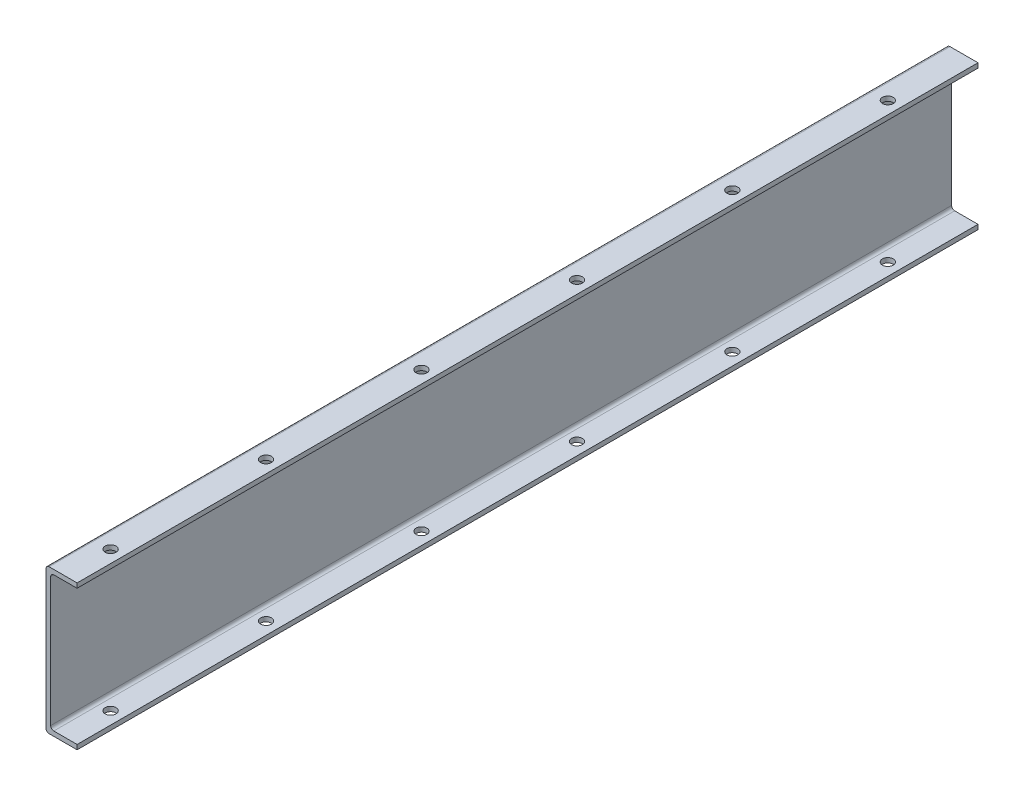
SolidWorks part; units mm, degrees
material "6061-T6 (SS)"
ref_plane "Front Plane" through (0, 0, 0) normal (0, 0, 1) x (1, 0, 0)
ref_plane "Top Plane" through (0, 0, 0) normal (0, 1, 0) x (1, 0, 0)
ref_plane "Right Plane" through (0, 0, 0) normal (1, 0, 0) x (0, 0, -1)
sketch "Sketch1" plane through (0, 0, 0) normal (0, 0, 1) x (1, 0, 0)
  line L1 (-0.75, 21.75) -> (0.75, 21.75)
  line L2 (-0.75, 21.75) -> (-0.75, -21.75)
  line L3 (-0.75, -21.75) -> (0.75, -21.75)
  line L4 (0.75, 21.75) -> (0.75, -21.75)
  line L5 (-0.75, 21.75) -> (9.25, 21.75)
  line L6 (-0.75, 21.75) -> (-0.75, 23.25)
  line L7 (-0.75, 23.25) -> (9.25, 23.25)
  line L8 (9.25, 21.75) -> (9.25, 23.25)
  line L9 (-0.75, -21.75) -> (9.25, -21.75)
  line L10 (-0.75, -21.75) -> (-0.75, -23.25)
  line L11 (-0.75, -23.25) -> (9.25, -23.25)
  line L12 (9.25, -21.75) -> (9.25, -23.25)
  dimension "D1" = 43.5
  dimension "D2" = 1.5
  dimension "D3" = 0.75
  dimension "D4" = 21.75
  dimension "D5" = 1.5
  dimension "D6" = 10
  dimension "D7" = 1.5
  dimension "D8" = 10
extrude "Boss-Extrude1" add sketch "Sketch1" along normal blind 289.77 contours L4 L1 L2 L3 | L5 L8 L7 L6 L1 | L12 L9 L3 L10 L11
fillet "Fillet1" radius 1 4 edges at (0.75, -21.75, 144.885) (0.75, 21.75, 144.885) (-0.75, 23.25, 144.885) (-0.75, -23.25, 144.885)
sketch "Sketch3" plane through (0, -23.25, 0) normal (0, -1, 0) x (-1, 0, 0)
  line L0 (-5.25, 0) -> (-5.25, -289.77) construction
  line L1 (-0.25, 0) -> (-9.25, 0) construction
  line L2 (-0.25, -289.77) -> (-9.25, -289.77) construction
  line L4 (-0.25, -289.77) -> (-0.25, 0) construction
  circle A0 centre (-5.25, -25) radius 1.75
  circle A1 centre (-5.25, -75) radius 1.75
  circle A2 centre (-5.25, -125) radius 1.75
  circle A3 centre (-5.25, -175) radius 1.75
  circle A4 centre (-5.25, -225) radius 1.75
  circle A5 centre (-5.25, -275) radius 1.75
  dimension "D2" = 3.5
  dimension "D3" = 3.5
  dimension "D4" = 3.5
  dimension "D5" = 3.5
  dimension "D6" = 3.5
  dimension "D7" = 3.5
  dimension "D8" = 50
  dimension "D9" = 25
  dimension "D10" = 50
  dimension "D11" = 50
  dimension "D12" = 50
  dimension "D13" = 50
  dimension "D14" = 5
extrude "Cut-Extrude1" cut sketch "Sketch3" against normal blind 246.38
